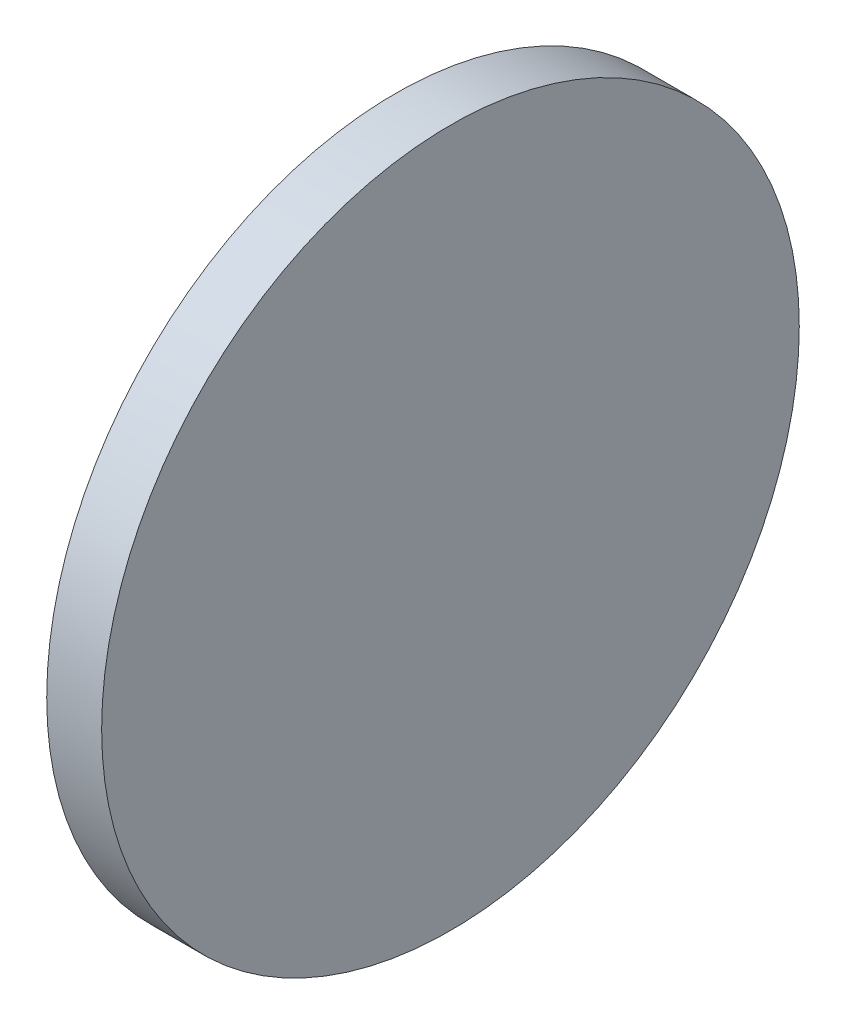
SolidWorks part; units mm, degrees
ref_plane "前视基准面" through (0, 0, 0) normal (0, 0, 1) x (1, 0, 0)
ref_plane "上视基准面" through (0, 0, 0) normal (0, 1, 0) x (1, 0, 0)
ref_plane "右视基准面" through (0, 0, 0) normal (1, 0, 0) x (0, 0, -1)
sketch "草图1" plane through (0, 0, 0) normal (0, 0, 1) x (1, 0, 0)
  line L0 (168.2475, 57.3101) -> (187.0435, 57.3101) construction
  line L1 (173.8774, 57.3101) -> (173.8774, 70.0101)
  line L2 (175.8774, 57.3101) -> (175.8774, 70.0101)
  line L3 (173.8774, 57.3101) -> (175.8774, 57.3101)
  line L5 (173.8774, 70.0101) -> (175.8774, 70.0101)
revolve "旋转1" add sketch "草图1" angle 360 about L0
